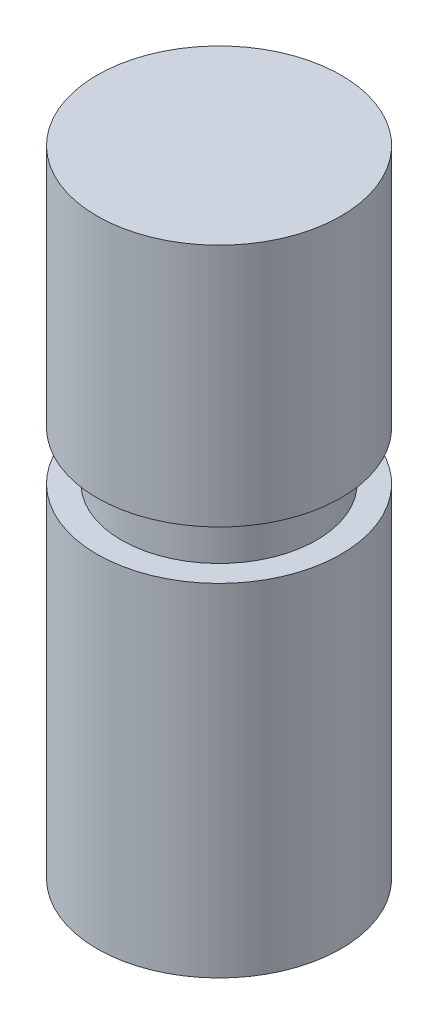
SolidWorks part; units mm, degrees
ref_plane "前视基准面" through (0, 0, 0) normal (0, 0, 1) x (1, 0, 0)
ref_plane "上视基准面" through (0, 0, 0) normal (0, 1, 0) x (1, 0, 0)
ref_plane "右视基准面" through (0, 0, 0) normal (1, 0, 0) x (0, 0, -1)
ref_plane "基准面1" through (0, 50, 0) normal (0, 1, 0) x (1, 0, 0)
ref_plane "基准面2" through (0, -10, 0) normal (0, 1, 0) x (1, 0, 0)
ref_plane "基准面3" through (0, -80, 0) normal (0, 1, 0) x (1, 0, 0)
ref_plane "基准面4" through (0, -10, 0) normal (0, 1, 0) x (1, 0, 0)
sketch "草图4" plane through (0, 50, 0) normal (0, 1, 0) x (1, 0, 0)
  circle A0 centre (0, 0) radius 25
sketch "草图5" plane through (0, -10, 0) normal (0, 1, 0) x (1, 0, 0)
  circle A0 centre (0, 0) radius 20
sketch "草图6" plane through (0, -80, 0) normal (0, 1, 0) x (1, 0, 0)
  circle A0 centre (0, 0) radius 25
extrude "凸台-拉伸1" add sketch "草图4" against normal blind 50
extrude "凸台-拉伸2" add sketch "草图5" along normal blind 50
extrude "凸台-拉伸3" add sketch "草图6" along normal blind 70 contours A0
sketch "草图8" plane through (0, 0, 0) normal (0, 0, 1) x (1, 0, 0)
  line L0 (42.1947, -80) -> (-42.1947, -80) construction
  line L1 (138.3239, -203.8043) -> (135.7205, -199.8074) construction
  spline S0 degree 3 poles (27.5, -80) (31.3959, -157.2619) (5.0163, -160.4077) (-27.5, -185.1561) knots 0 0 0 0 1 1 1 1
  spline S1 degree 3 poles (-27.5, -185.1561) (-42.8894, -202.116) (-34.886, -238.9299) (2.5815, -253.3958) (30.5053, -247.9512) (50.0775, -232.08) (77.3282, -205.7776) (106.4884, -194.6989) (130.1712, -197.9745) knots 0 0 0 0 0.272254 0.368702 0.502523 0.622911 0.694296 1 1 1 1
  spline S2 degree 3 poles (137.0222, -201.8059) (138.6493, -204.304) (140.1507, -212.1129) (125.1448, -221.1768) (109.8343, -236.7684) (96.7237, -265.5965) (75.4751, -283.1449) (54.8757, -302.0352) (30.4659, -311.6043) (1.0547, -321.4564) (-23.4803, -314.4305) (-42.5869, -309.1576) (-57.297, -298.9559) (-71.4859, -286.448) (-88.8251, -259.4527) (-106.296, -209.2235) (-81.6856, -166.7678) (-65.309, -149.2647) knots 0.018423 0.018423 0.018423 0.018423 0.038146 0.065651 0.127006 0.195515 0.280874 0.317312 0.390226 0.462614 0.527911 0.563805 0.600955 0.651836 0.695134 0.825323 1 1 1 1
  spline S3 degree 3 poles (-65.309, -149.2647) (-54.8038, -138.6192) (-33.9494, -119.1739) (-27.5905, -91.7151) (-27.5, -80) knots 0 0 0 0 0.566538 1 1 1 1
  point P0 (0, -80)
  point P10 (-27.5, -80)
ref_plane "5" through (0, -110, 0) normal (0, 1, 0) x (1, 0, 0)
sketch "草图10" plane through (0, 0, 0) normal (0, 0, 1) x (1, 0, 0)
  line L0 (0, 0) -> (0, -276.9201) construction
  point P0 (0, -216.7842)
ref_plane "6" through (0, -216.7842, 0) normal (0, 1, 0) x (1, 0, 0)
sketch "草图11" plane through (0, -216.7842, 0) normal (0, 1, 0) x (1, 0, 0)
  line L0 (0, 37.4736) -> (0, -39.244)
sketch "草图14" plane through (0, -110, 0) normal (0, 1, 0) x (1, 0, 0)
  circle A0 centre (-27.5, -0.0001) radius 0.0001
sketch "草图15" plane through (0, -80, 0) normal (0, 1, 0) x (1, 0, 0)
  circle A0 centre (0, 0) radius 27.5
